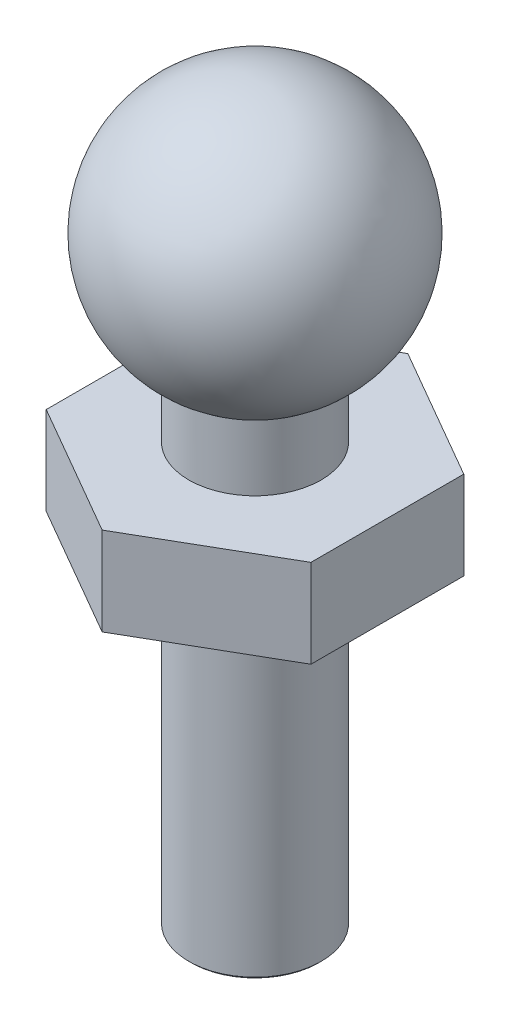
SolidWorks part; units mm, degrees
ref_plane "Front Plane" through (0, 0, 0) normal (0, 0, 1) x (1, 0, 0)
ref_plane "Top Plane" through (0, 0, 0) normal (0, 1, 0) x (1, 0, 0)
ref_plane "Right Plane" through (0, 0, 0) normal (1, 0, 0) x (0, 0, -1)
sketch "Sketch1" plane through (0, 0, 0) normal (0, 0, 1) x (1, 0, 0)
  line L0 (0, 0) -> (0, 16.5981) construction
  line L1 (0, 0) -> (1.5, 0)
  line L2 (1.5, 0) -> (1.5, 11)
  line L3 (0, 0) -> (0, 16.5981)
  arc A0 (0, 16.5981) -> (1.5, 11) centre (0, 13.5981) cw
  point P6 (0, 0)
  dimension "D1" = 11
  dimension "D3" = 3
  dimension "D2" = 1.5
revolve "Revolve1" add sketch "Sketch1" angle 360 about L0
sketch "Sketch2" plane through (0, 0, 0) normal (0, 0, 1) x (1, 0, 0)
  line L0 (-4.5696, 7.5) -> (7.3959, 7.5)
  dimension "D1" = 7.5
split line "Split Line1"
fillet "Fillet1" [suppressed] radius 0.5
chamfer "Chamfer1" distance 0.05 angle 45 1 edges at (0, 0, -1.5)
ref_plane "Plane1" through (0, 7.5, 0) normal (0, 1, 0) x (1, 0, 0)
sketch "Sketch3" plane through (0, 7.5, 0) normal (0, 1, 0) x (1, 0, 0)
  line L1 (3, 1.7321) -> (0, 3.4641)
  line L2 (0, 3.4641) -> (-3, 1.7321)
  line L3 (-3, 1.7321) -> (-3, -1.7321)
  line L4 (-3, -1.7321) -> (0, -3.4641)
  line L5 (0, -3.4641) -> (3, -1.7321)
  line L6 (3, -1.7321) -> (3, 1.7321)
  circle A0 centre (0, 0) radius 3 construction
  circle A1 centre (0, 0) radius 1.5 construction
  circle A2 centre (0, 0) radius 1.5
  point P1 (0, 0)
  point P10 (0, 0)
  point P11 (0, 0)
  point P12 (11.5922, -5.1801)
  dimension "D1" = 6
extrude "Boss-Extrude1" add sketch "Sketch3" along normal blind 2
